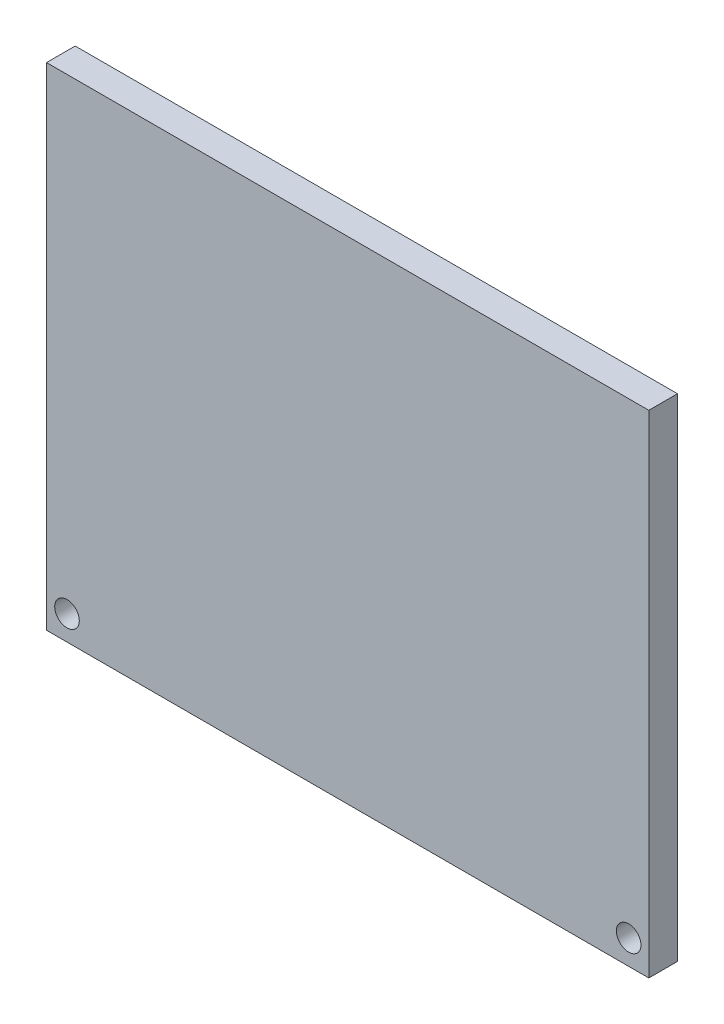
SolidWorks part; units mm, degrees
material "Acrílico (médio-alto impacto)"
ref_plane "Plano frontal" through (0, 0, 0) normal (0, 0, 1) x (1, 0, 0)
ref_plane "Plano superior" through (0, 0, 0) normal (0, 1, 0) x (1, 0, 0)
ref_plane "Plano direito" through (0, 0, 0) normal (1, 0, 0) x (0, 0, -1)
sketch "Esboço1" plane through (0, 0, 0) normal (0, 0, 1) x (1, 0, 0)
  line L1 (-73.5, 60) -> (73.5, 60)
  line L2 (-73.5, 60) -> (-73.5, -60)
  line L3 (-73.5, -60) -> (73.5, -60)
  line L4 (73.5, 60) -> (73.5, -60)
  line L5 (-73.5, 60) -> (73.5, -60) construction
  line L6 (-73.5, -60) -> (73.5, 60) construction
  circle A0 centre (-68.5, -54) radius 3
  circle A1 centre (68.58, -54) radius 3
  point P0 (0, 0)
  dimension "D3" = 6
  dimension "D4" = 6
  dimension "D5" = 6
  dimension "D6" = 6
  dimension "D7" = 5
  dimension "D8" = 137.08
  dimension "D1" = 147
  dimension "D2" = 120
extrude "Ressalto-extrusão1" add sketch "Esboço1" along normal blind 7
